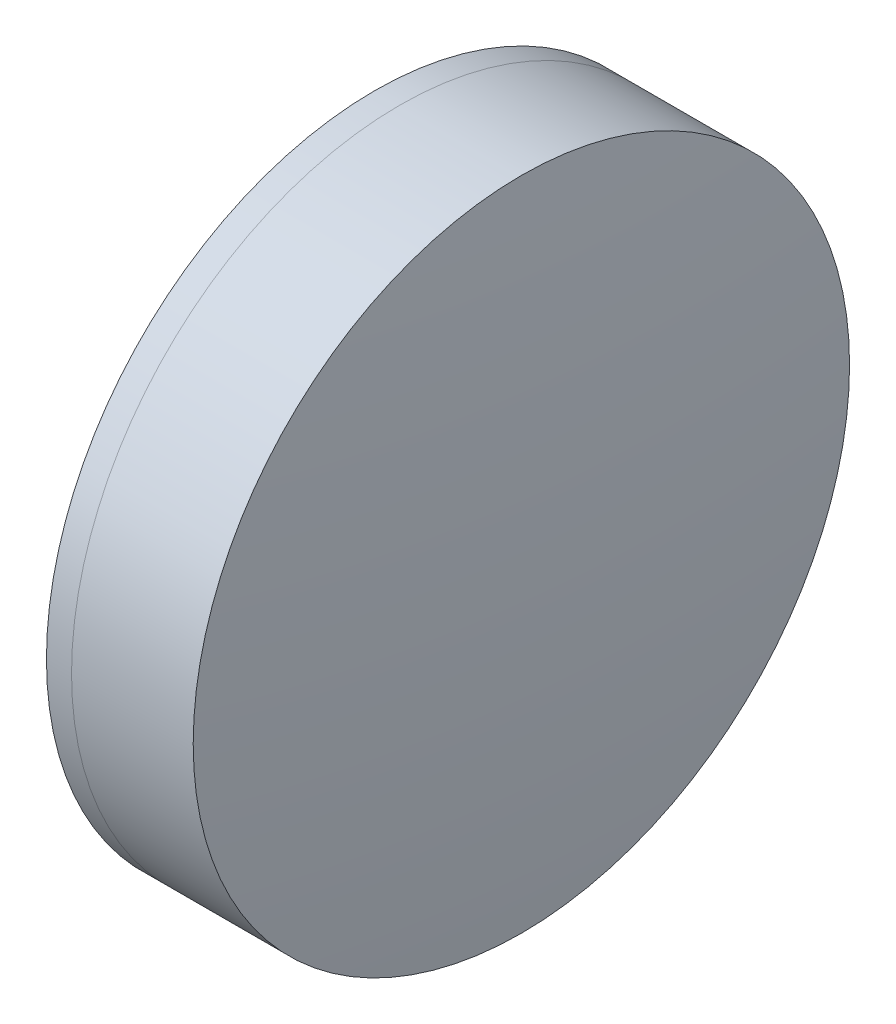
SolidWorks part; units mm, degrees
ref_plane "前视基准面" through (0, 0, 0) normal (0, 0, 1) x (1, 0, 0)
ref_plane "上视基准面" through (0, 0, 0) normal (0, 1, 0) x (1, 0, 0)
ref_plane "右视基准面" through (0, 0, 0) normal (1, 0, 0) x (0, 0, -1)
sketch "草图1" plane through (0, 0, 0) normal (0, 1, 0) x (1, 0, 0)
  line L0 (-9.7026, 0) -> (238.8542, 0) construction
  line L1 (232.6976, -12.7) -> (233.6684, -12.7)
  line L2 (232.6976, 12.7) -> (233.6684, 12.7)
  arc A0 (233.6684, -12.7) -> (233.6684, 12.7) centre (211.0958, 0) ccw
  arc A1 (232.6976, 12.7) -> (232.6976, -12.7) centre (261.1958, 0) ccw
  point P10 (229.9958, 0)
  point P11 (236.9958, 0)
  dimension "D3" = 31.2
  dimension "D4" = 25.9
  dimension "D1" = 12.7
  dimension "D2" = 12.7
  dimension "D5" = 7
revolve "旋转1" add sketch "草图1" angle 360 about L0
sketch "草图2" plane through (0, 0, 0) normal (0, 1, 0) x (1, 0, 0)
  line L0 (-0.5519, 0) -> (253.9868, 0) construction
  line L2 (233.6684, 12.7) -> (238.3769, 12.7)
  line L3 (233.6684, -12.7) -> (238.3769, -12.7)
  arc A0 (238.3769, -12.7) -> (238.3769, 12.7) centre (108.3958, 0) ccw
  arc A1 (233.6684, -12.7) -> (233.6684, 12.7) centre (211.0958, 0) ccw construction
  arc A2 (233.6684, -12.7) -> (233.6684, 12.7) centre (211.0958, 0) ccw
  point P4 (236.9958, 0)
  point P8 (238.9958, 0)
  dimension "D1" = 130.6
  dimension "D2" = 2
revolve "旋转3" add sketch "草图2" angle 360 about L0
